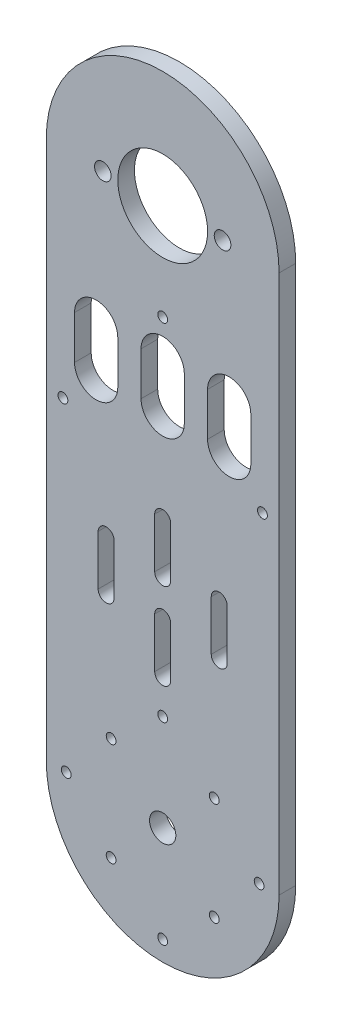
SolidWorks part; units mm, degrees
ref_plane "Front Plane" through (0, 0, 0) normal (0, 0, 1) x (1, 0, 0)
ref_plane "Top Plane" through (0, 0, 0) normal (0, 1, 0) x (1, 0, 0)
ref_plane "Right Plane" through (0, 0, 0) normal (1, 0, 0) x (0, 0, -1)
sketch "Sketch1" plane through (0, 0, 0) normal (0, 0, 1) x (1, 0, 0)
  line L0 (35, 0) -> (35, 162)
  line L1 (-35, 0) -> (-35, 162)
  line L2 (-35, 162) -> (35, 162) construction
  line L3 (0, 0) -> (35, 0) construction
  line L4 (0, 0) -> (0, 39.5) construction
  line L5 (0, 0) -> (25.0676, 25.0676) construction
  line L6 (0, 0) -> (0, 162) construction
  line L7 (0, 54.5) -> (0, 39.5) construction
  line L8 (2.4, 54.5) -> (2.4, 39.5)
  line L9 (-2.4, 54.5) -> (-2.4, 39.5)
  line L10 (0, 80.5) -> (0, 65.5) construction
  line L11 (2.4, 80.5) -> (2.4, 65.5)
  line L12 (-2.4, 80.5) -> (-2.4, 65.5)
  line L13 (17, 67.5) -> (17, 52.5) construction
  line L14 (19.4, 67.5) -> (19.4, 52.5)
  line L15 (14.6, 67.5) -> (14.6, 52.5)
  line L16 (-17, 67.5) -> (-17, 52.5) construction
  line L17 (-19.4, 67.5) -> (-19.4, 52.5)
  line L18 (-14.6, 67.5) -> (-14.6, 52.5)
  line L19 (0, 121.5) -> (0, 108.5) construction
  line L20 (6.5, 121.5) -> (6.5, 108.5)
  line L21 (-6.5, 121.5) -> (-6.5, 108.5)
  line L22 (20, 120.9465) -> (20, 107.9465) construction
  line L23 (26.5, 120.9465) -> (26.5, 107.9465)
  line L24 (13.5, 120.9465) -> (13.5, 107.9465)
  line L25 (-20, 120.9465) -> (-20, 107.9465) construction
  line L26 (-26.5, 120.9465) -> (-26.5, 107.9465)
  line L27 (-13.5, 120.9465) -> (-13.5, 107.9465)
  arc A0 (-35, 0) -> (35, 0) centre (0, 0) ccw
  arc A1 (35, 162) -> (-35, 162) centre (0, 162) ccw
  circle A2 centre (0, 0) radius 3.95
  circle A3 centre (15.5, 15.5) radius 1.475
  circle A4 centre (15.5, -15.5) radius 1.475
  circle A5 centre (-15.5, -15.5) radius 1.475
  circle A6 centre (-15.5, 15.5) radius 1.475
  arc A7 (2.4, 54.5) -> (-2.4, 54.5) centre (0, 54.5) ccw
  arc A8 (-2.4, 39.5) -> (2.4, 39.5) centre (0, 39.5) ccw
  circle A9 centre (0, 29) radius 1.475
  arc A10 (2.4, 80.5) -> (-2.4, 80.5) centre (0, 80.5) ccw
  arc A11 (-2.4, 65.5) -> (2.4, 65.5) centre (0, 65.5) ccw
  arc A12 (19.4, 67.5) -> (14.6, 67.5) centre (17, 67.5) ccw
  arc A13 (14.6, 52.5) -> (19.4, 52.5) centre (17, 52.5) ccw
  arc A14 (-19.4, 67.5) -> (-14.6, 67.5) centre (-17, 67.5) cw
  arc A15 (-14.6, 52.5) -> (-19.4, 52.5) centre (-17, 52.5) cw
  arc A16 (6.5, 121.5) -> (-6.5, 121.5) centre (0, 121.5) ccw
  arc A17 (-6.5, 108.5) -> (6.5, 108.5) centre (0, 108.5) ccw
  arc A18 (26.5, 120.9465) -> (13.5, 120.9465) centre (20, 120.9465) ccw
  arc A19 (13.5, 107.9465) -> (26.5, 107.9465) centre (20, 107.9465) ccw
  arc A20 (-26.5, 120.9465) -> (-13.5, 120.9465) centre (-20, 120.9465) cw
  arc A21 (-13.5, 107.9465) -> (-26.5, 107.9465) centre (-20, 107.9465) cw
  circle A22 centre (0, 162) radius 13.5
  circle A23 centre (-18, 162) radius 2.5
  circle A24 centre (18, 162) radius 2.5
  circle A25 centre (0, 133) radius 1.475
  circle A26 centre (-30, 97) radius 1.475
  circle A27 centre (30, 97) radius 1.475
  circle A28 centre (29, 0) radius 1.475
  circle A29 centre (0, -29) radius 1.475
  circle A30 centre (-29, 0) radius 1.475
  point P13 (0, 47)
  point P21 (0, 0)
  point P27 (0, 73)
  point P36 (17, 60)
  point P41 (0, 115)
  point P44 (-17, 60)
  point P55 (20, 114.4465)
  point P65 (-20, 114.4465)
  point P89 (0, 0)
  dimension "D1" = 70
  dimension "D4" = 7.9
  dimension "D6" = 2.95
  dimension "D11" = 2.4
  dimension "D12" = 2.95
  dimension "D16" = 2.4
  dimension "D18" = 2.4
  dimension "D22" = 6.5
  dimension "D24" = 6.5
  dimension "D27" = 27
  dimension "D28" = 5
  dimension "D30" = 2.95
  dimension "D32" = 2.95
  dimension "D2" = 162
  dimension "D3" = 162
  dimension "D5" = 45
  dimension "D7" = 15.5
  dimension "D9" = 39.5
  dimension "D10" = 15
  dimension "D13" = 29
  dimension "D14" = 11
  dimension "D15" = 15
  dimension "D17" = 18
  dimension "D19" = 15
  dimension "D20" = 60
  dimension "D21" = 13
  dimension "D23" = 40.5
  dimension "D25" = 13
  dimension "D26" = 7
  dimension "D29" = 18
  dimension "D31" = 29
  dimension "D33" = 65
  dimension "D34" = 5
  dimension "D8" = 4
  dimension "D35" = 4
extrude "Boss-Extrude1" add sketch "Sketch1" along normal blind 5
